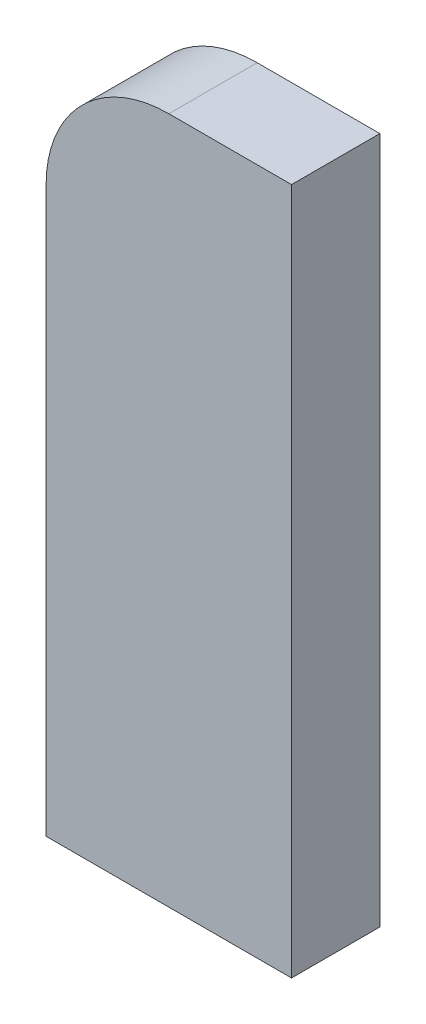
SolidWorks part; units mm, degrees
ref_plane "Front Plane" through (0, 0, 0) normal (0, 0, 1) x (1, 0, 0)
ref_plane "Top Plane" through (0, 0, 0) normal (0, 1, 0) x (1, 0, 0)
ref_plane "Right Plane" through (0, 0, 0) normal (1, 0, 0) x (0, 0, -1)
sketch "Sketch1" plane through (0, 0, 0) normal (0, 0, 1) x (1, 0, 0)
  line L1 (0, 0) -> (25, 0)
  line L2 (0, 0) -> (0, 57.5)
  line L3 (12.5, 70) -> (25, 70)
  line L4 (25, 0) -> (25, 70)
  arc A0 (12.5, 70) -> (0, 57.5) centre (12.5, 57.5) ccw
  point P7 (0, 70)
  dimension "D3" = 12.5
  dimension "D1" = 25
  dimension "D2" = 70
extrude "Boss-Extrude1" add sketch "Sketch1" along normal blind 9
